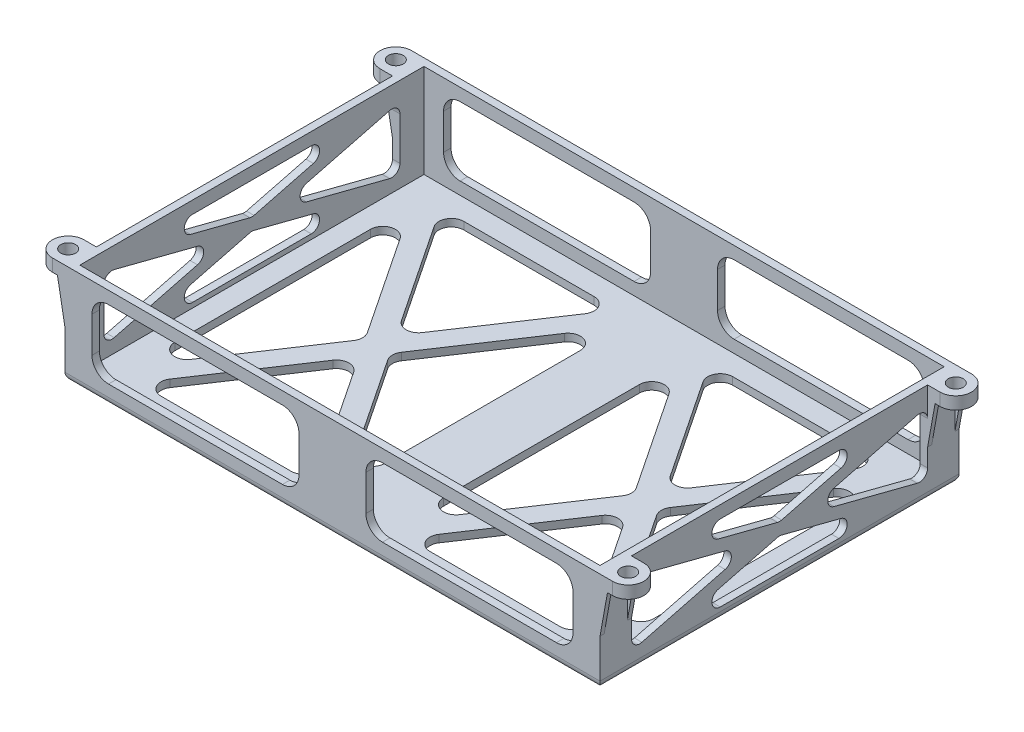
SolidWorks part; units mm, degrees
other "Markup2"
sketch "Sketch32" plane through (-159.4724, 0, 108) normal (-0.262, -0.0774, 0.962) x (0.8638, -0.4632, 0.198)
ref_plane "Front Plane" through (0, 0, 0) normal (0, 0, 1) x (1, 0, 0)
ref_plane "Top Plane" through (0, 0, 0) normal (0, 1, 0) x (1, 0, 0)
ref_plane "Right Plane" through (0, 0, 0) normal (1, 0, 0) x (0, 0, -1)
sketch "Sketch1" plane through (0, 0, 0) normal (0, 1, 0) x (1, 0, 0)
  line L0 (-2.286, -2.286) -> (-2.286, -107.823) construction
  line L1 (0, 0) -> (-164.084, 0)
  line L2 (0, 0) -> (0, -110.109)
  line L3 (0, -110.109) -> (-164.084, -110.109)
  line L4 (-164.084, 0) -> (-164.084, -110.109)
  line L5 (-2.286, -107.823) -> (-161.798, -107.823) construction
  line L6 (-161.798, -2.286) -> (-161.798, -107.823) construction
  line L7 (-2.286, -2.286) -> (-161.798, -2.286) construction
  dimension "D1" = 2.286
  dimension "D2" = 105.537
  dimension "D3" = 159.512
extrude "Boss-Extrude1" add sketch "Sketch1" along normal blind 30.988 contours L1 L4 L3 L2
shell "Shell1" thickness 2.286
sketch "Sketch7" plane through (0, 30.988, 0) normal (0, 1, 0) x (1, 0, 0)
  line L0 (-167.894, 0) -> (-164.084, 0)
  line L1 (-164.084, 0) -> (-164.084, -9.652)
  line L2 (-164.084, 0) -> (-164.084, -110.109) construction
  line L3 (-164.084, -9.652) -> (-167.894, -9.652)
  line L4 (-82.042, -1000) -> (-82.042, 49000) construction
  line L5 (0, 0) -> (-164.084, 0) construction
  line L6 (-1150, -55.0545) -> (48850, -55.0545) construction
  line L7 (-161.798, -2.286) -> (-161.798, -107.823) construction
  line L8 (-164.084, -100.457) -> (-167.894, -100.457)
  line L9 (-164.084, -110.109) -> (-164.084, -100.457)
  line L10 (-167.894, -110.109) -> (-164.084, -110.109)
  line L11 (3.81, -110.109) -> (0, -110.109)
  line L12 (0, -110.109) -> (0, -100.457)
  line L13 (0, -100.457) -> (3.81, -100.457)
  line L14 (0, -9.652) -> (3.81, -9.652)
  line L15 (0, 0) -> (0, -9.652)
  line L16 (3.81, 0) -> (0, 0)
  circle A0 centre (-167.894, -4.826) radius 2.286
  arc A2 (-167.894, 0) -> (-167.894, -9.652) centre (-167.894, -4.826) ccw
  arc A3 (-167.894, -110.109) -> (-167.894, -100.457) centre (-167.894, -105.283) cw
  circle A4 centre (-167.894, -105.283) radius 2.286
  circle A5 centre (3.81, -105.283) radius 2.286
  arc A6 (3.81, -110.109) -> (3.81, -100.457) centre (3.81, -105.283) ccw
  arc A7 (3.81, 0) -> (3.81, -9.652) centre (3.81, -4.826) cw
  circle A8 centre (3.81, -4.826) radius 2.286
  point P14 (-82.042, 0)
  point P19 (-161.798, -55.0545)
  dimension "D1" = 2.54
  dimension "D3" = 4.572
  dimension "D2" = 3.81
extrude "Boss-Extrude7" add sketch "Sketch7" against normal blind 3.81
ref_plane "Plane1" through (0, 0, 55.0545) normal (0, 0, -1) x (-1, 0, 0)
ref_plane "Plane2" through (-82.042, 0, 0) normal (-1, 0, 0) x (0, 0, 1)
sketch "Sketch33" plane through (0, 0, 0) normal (1, 0, 0) x (0, 0, -1)
  line L0 (-9.652, 27.178) -> (-100.457, 3.81) construction
  line L1 (-9.652, 27.178) -> (-100.457, 27.178)
  line L2 (-9.652, 27.178) -> (-9.652, 3.81)
  line L3 (-9.652, 3.81) -> (-100.457, 3.81)
  line L4 (-100.457, 27.178) -> (-100.457, 3.81)
  line L5 (-9.652, 3.81) -> (-100.457, 27.178) construction
  line L6 (-9.652, 27.178) -> (-9.652, 30.988) construction
  line L7 (-55.0545, 17.3299) -> (-93.3228, 27.178)
  line L8 (-9.652, 30.988) -> (-100.457, 30.988) construction
  line L10 (0, 27.178) -> (-9.652, 27.178) construction
  line L11 (-55.0545, 13.6581) -> (-93.3228, 3.81)
  line L12 (0, 0) -> (-110.109, 0) construction
  line L13 (-9.652, 5.6459) -> (-47.9203, 15.494)
  line L14 (-16.7862, 27.178) -> (-55.0545, 17.3299)
  line L15 (-16.7862, 3.81) -> (-55.0545, 13.6581)
  line L16 (-9.652, 25.3421) -> (-47.9203, 15.494)
  line L17 (-9.2089, 25.4561) -> (-100.0139, 2.0881) construction
  line L18 (-10.0951, 28.8999) -> (-100.9001, 5.5319) construction
  line L19 (-9.2089, 5.5319) -> (-100.0139, 28.8999) construction
  line L20 (-10.0951, 2.0881) -> (-100.9001, 25.4561) construction
  line L21 (-62.1887, 15.494) -> (-100.457, 5.6459)
  line L22 (-62.1887, 15.494) -> (-100.457, 25.3421)
  point P10 (-55.0545, 30.988)
  point P12 (-55.0545, 27.178)
  dimension "D1" = 3.81
  dimension "D2" = 1.778
  dimension "D3" = 1.778
extrude "Cut-Extrude1" cut sketch "Sketch33" against normal up to surface (161.798 mm away) contours L3 L15 L11 | L2 L16 L13 | L21 L22 L4 | L14 L1 L7
fillet "Fillet1" radius 2.54 12 edges at (-1.143, 3.81, 16.7862) (-1.143, 13.6581, 55.0545) (-1.143, 3.81, 93.3228) (-1.143, 5.6459, 100.457) (-1.143, 25.3421, 100.457) (-1.143, 15.494, 62.1887) (-1.143, 17.3299, 55.0545) (-1.143, 27.178, 93.3228) (-1.143, 27.178, 16.7862) (-1.143, 5.6459, 9.652) (-1.143, 25.3421, 9.652) (-1.143, 15.494, 47.9203)
mirror "Mirror1" about plane through (-82.042, 0, 0) normal (-1, 0, 0) of "Fillet1", "Cut-Extrude1"
sketch "Sketch34" plane through (0, 0, 107.823) normal (0, 0, -1) x (-1, 0, 0)
  line L0 (92.298, 16.637) -> (71.786, 16.637) construction
  line L1 (150.718, 6.096) -> (97.378, 6.096)
  line L2 (155.798, 11.176) -> (155.798, 22.098)
  line L3 (150.718, 27.178) -> (97.378, 27.178)
  line L4 (92.298, 11.176) -> (92.298, 22.098)
  line L5 (66.706, 6.096) -> (13.366, 6.096)
  line L6 (71.786, 11.176) -> (71.786, 22.098)
  line L7 (66.706, 27.178) -> (13.366, 27.178)
  line L8 (8.286, 11.176) -> (8.286, 22.098)
  line L9 (2.286, 30.988) -> (161.798, 30.988) construction
  line L10 (161.798, 30.988) -> (161.798, 2.286) construction
  line L11 (2.286, 2.286) -> (161.798, 2.286) construction
  arc A0 (150.718, 6.096) -> (155.798, 11.176) centre (150.718, 11.176) ccw
  arc A1 (155.798, 22.098) -> (150.718, 27.178) centre (150.718, 22.098) ccw
  arc A2 (97.378, 27.178) -> (92.298, 22.098) centre (97.378, 22.098) ccw
  arc A3 (97.378, 6.096) -> (92.298, 11.176) centre (97.378, 11.176) cw
  arc A4 (13.366, 6.096) -> (8.286, 11.176) centre (13.366, 11.176) cw
  arc A5 (66.706, 6.096) -> (71.786, 11.176) centre (66.706, 11.176) ccw
  arc A6 (71.786, 22.098) -> (66.706, 27.178) centre (66.706, 22.098) ccw
  arc A7 (13.366, 27.178) -> (8.286, 22.098) centre (13.366, 22.098) ccw
  point P12 (82.042, 30.988)
  point P13 (82.042, 16.637)
  point P16 (161.798, 16.637)
  point P17 (155.798, 16.637)
  point P30 (8.286, 6.096)
  point P33 (71.786, 6.096)
  dimension "D4" = 5.08
  dimension "D1" = 6
  dimension "D2" = 63.5
  dimension "D3" = 3.81
extrude "Cut-Extrude2" cut sketch "Sketch34" against normal through all both and the other way through all
fillet "Fillet2" radius 2.54 4 edges at (-82.042, 0, 0) (-164.084, 0, 55.0545) (-82.042, 0, 110.109) (0, 0, 55.0545)
sketch "Sketch36" plane through (0, 2.286, 0) normal (0, 1, 0) x (1, 0, 0)
  line L0 (-103.2935, -8.636) -> (-143.2465, -8.636)
  line L2 (-164.084, 0) -> (-164.084, -110.109) construction
  line L4 (-151.638, -97.663) -> (-94.902, -12.446) construction
  line L6 (-91.092, -85.059) -> (-91.092, -25.05)
  line L7 (-151.638, -12.446) -> (-94.902, -97.663) construction
  line L9 (0, 0) -> (-164.084, 0) construction
  line L11 (-164.084, -110.109) -> (0, -110.109) construction
  line L14 (-155.448, -25.05) -> (-155.448, -85.059)
  line L15 (-143.2465, -101.473) -> (-103.2935, -101.473)
  line L16 (-155.6918, -103.7518) -> (-93.6147, -10.5125) construction
  line L17 (-82.042, -1089.6267) -> (-82.042, 48910.3733) construction
  line L18 (-148.4666, -22.9385) -> (-128.4901, -52.943)
  line L19 (-146.4179, -95.5515) -> (-126.4414, -65.547)
  line L22 (-146.4179, -14.5575) -> (-126.4414, -44.562)
  line L23 (-148.4666, -87.1705) -> (-128.4901, -57.166)
  line L26 (-148.9952, -10.6864) -> (-92.2592, -95.9034) construction
  line L27 (-154.2808, -14.2056) -> (-97.5448, -99.4226) construction
  line L28 (-153.049, -105.5114) -> (-90.9719, -12.272) construction
  line L29 (-158.3347, -101.9923) -> (-96.2575, -8.7529) construction
  line L30 (-2.54, -107.569) -> (-161.544, -107.569) construction
  line L31 (-12.446, -12.446) -> (-69.182, -97.663) construction
  line L32 (-12.446, -97.663) -> (-69.182, -12.446) construction
  line L33 (-43.9854, -44.562) -> (-63.9619, -14.5575)
  line L38 (-118.0499, -52.943) -> (-98.0734, -22.9385)
  line L39 (-118.0499, -57.166) -> (-98.0734, -87.1705)
  line L40 (-120.0986, -65.547) -> (-100.1221, -95.5515)
  line L41 (-120.0986, -44.562) -> (-100.1221, -14.5575)
  line L42 (-43.9854, -65.547) -> (-63.9619, -95.5515)
  line L43 (-46.0341, -57.166) -> (-66.0106, -87.1705)
  line L44 (-46.0341, -52.943) -> (-66.0106, -22.9385)
  line L45 (-15.6174, -87.1705) -> (-35.5939, -57.166)
  line L46 (-17.6661, -14.5575) -> (-37.6426, -44.562)
  line L47 (-17.6661, -95.5515) -> (-37.6426, -65.547)
  line L48 (-15.6174, -22.9385) -> (-35.5939, -52.943)
  line L49 (-20.8375, -101.473) -> (-60.7905, -101.473)
  line L50 (-8.636, -25.05) -> (-8.636, -85.059)
  line L51 (-72.992, -85.059) -> (-72.992, -25.05)
  line L52 (-60.7905, -8.636) -> (-20.8375, -8.636)
  arc A12 (-146.4179, -14.5575) -> (-143.2465, -8.636) centre (-143.2465, -12.446) cw
  arc A13 (-100.1221, -14.5575) -> (-103.2935, -8.636) centre (-103.2935, -12.446) ccw
  arc A14 (-98.0734, -22.9385) -> (-91.092, -25.05) centre (-94.902, -25.05) cw
  arc A15 (-118.0499, -52.943) -> (-118.0499, -57.166) centre (-114.8785, -55.0545) ccw
  arc A16 (-98.0734, -87.1705) -> (-91.092, -85.059) centre (-94.902, -85.059) ccw
  arc A17 (-126.4414, -65.547) -> (-120.0986, -65.547) centre (-123.27, -67.6585) cw
  arc A18 (-100.1221, -95.5515) -> (-103.2935, -101.473) centre (-103.2935, -97.663) cw
  arc A19 (-146.4179, -95.5515) -> (-143.2465, -101.473) centre (-143.2465, -97.663) ccw
  arc A20 (-148.4666, -87.1705) -> (-155.448, -85.059) centre (-151.638, -85.059) cw
  arc A21 (-128.4901, -52.943) -> (-128.4901, -57.166) centre (-131.6615, -55.0545) cw
  arc A22 (-148.4666, -22.9385) -> (-155.448, -25.05) centre (-151.638, -25.05) ccw
  arc A23 (-120.0986, -44.562) -> (-126.4414, -44.562) centre (-123.27, -42.4505) cw
  arc A24 (-43.9854, -44.562) -> (-37.6426, -44.562) centre (-40.814, -42.4505) ccw
  arc A25 (-15.6174, -22.9385) -> (-8.636, -25.05) centre (-12.446, -25.05) cw
  arc A26 (-35.5939, -52.943) -> (-35.5939, -57.166) centre (-32.4225, -55.0545) ccw
  arc A27 (-15.6174, -87.1705) -> (-8.636, -85.059) centre (-12.446, -85.059) ccw
  arc A28 (-17.6661, -95.5515) -> (-20.8375, -101.473) centre (-20.8375, -97.663) cw
  arc A29 (-63.9619, -95.5515) -> (-60.7905, -101.473) centre (-60.7905, -97.663) ccw
  arc A30 (-37.6426, -65.547) -> (-43.9854, -65.547) centre (-40.814, -67.6585) ccw
  arc A31 (-66.0106, -87.1705) -> (-72.992, -85.059) centre (-69.182, -85.059) cw
  arc A32 (-46.0341, -52.943) -> (-46.0341, -57.166) centre (-49.2055, -55.0545) cw
  arc A33 (-66.0106, -22.9385) -> (-72.992, -25.05) centre (-69.182, -25.05) ccw
  arc A34 (-63.9619, -14.5575) -> (-60.7905, -8.636) centre (-60.7905, -12.446) cw
  arc A35 (-17.6661, -14.5575) -> (-20.8375, -8.636) centre (-20.8375, -12.446) ccw
  point P18 (-82.042, -107.569)
  point P87 (-119.4557, -55.0545)
  point P90 (-91.092, -97.6565)
  point P93 (-123.27, -60.7836)
  point P96 (-96.1797, -101.473)
  point P99 (-150.3603, -101.473)
  point P102 (-155.448, -97.6565)
  point P107 (-8.636, -97.6565)
  point P108 (-13.7237, -101.473)
  point P109 (-67.9043, -101.473)
  point P110 (-40.814, -60.7836)
  point P111 (-72.992, -97.6565)
  point P112 (-44.6283, -55.0545)
  dimension "D8" = 3.81
  dimension "D7" = 3.81
  dimension "D2" = 8.636
  dimension "D3" = 3.175
  dimension "D5" = 8.636
  dimension "D6" = 72.992
  dimension "D1" = 8.636
  dimension "D4" = 3.175
extrude "Cut-Extrude3" cut sketch "Sketch36" against normal through all
sketch "Sketch39" plane through (0, 0, 0) normal (0, 0, -1) x (-1, 0, 0)
  line L0 (166.37, 27.178) -> (164.084, 14.478)
  line L1 (164.084, 27.178) -> (164.084, 2.54) construction
  line L3 (164.084, 27.178) -> (167.894, 27.178) construction
  dimension "D1" = 12.7
  dimension "D2" = 2.286
sketch "Sketch40" plane through (0, 0, 9.652) normal (0, 0, 1) x (1, 0, 0)
  line L0 (-166.37, 27.178) -> (-164.084, 14.478) construction
  line L1 (-166.37, 27.178) -> (-164.084, 14.478)
rib "Rib1" sketch "Sketch40" sketch "Sketch40" thickness 1.27 extrusion direction parallel to sketch draft on no parameters "D1"=1.27
rib "Rib2" sketch "Sketch39" sketch "Sketch39" thickness 1.27 extrusion direction parallel to sketch draft on no parameters "D1"=1.27
mirror "Mirror2" about plane through (0, 0, 55.0545) normal (0, 0, -1) of "Rib1", "Rib2"
mirror "Mirror3" about plane through (-82.042, 0, 0) normal (-1, 0, 0) of "Mirror2", "Rib1", "Rib2"
